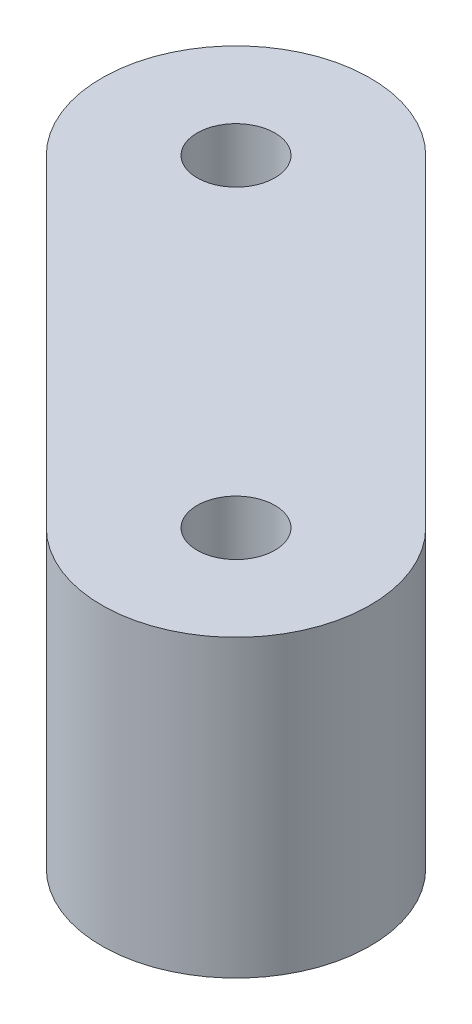
SolidWorks part; units mm, degrees
ref_plane "Alzado" through (0, 0, 0) normal (0, 0, 1) x (1, 0, 0)
ref_plane "Planta" through (0, 0, 0) normal (0, 1, 0) x (1, 0, 0)
ref_plane "Vista lateral" through (0, 0, 0) normal (1, 0, 0) x (0, 0, -1)
sketch "Croquis1" plane through (0, -33.4006, 0) normal (0, 1, 0) x (1, 0, 0)
  line L0 (-39.246, -103.383) -> (-20.7585, -84.8955) construction
  line L1 (-33.2356, -109.3934) -> (-45.2564, -97.3726) construction
  line L2 (-39.246, -103.383) -> (-42.0745, -100.5546) construction
  line L3 (-42.0745, -100.5546) -> (-35.0034, -93.4835) construction
  line L4 (-38.1854, -90.3015) -> (-26.1646, -102.3223) construction
  line L5 (-35.0034, -93.4835) -> (-29.3465, -99.1403) construction
  line L6 (-29.3465, -99.1403) -> (-36.4176, -106.2114) construction
  line L7 (-36.4176, -106.2114) -> (-42.0745, -100.5546) construction
  line L10 (-45.2564, -97.3726) -> (-33.2356, -109.3934)
  line L11 (-26.1646, -102.3223) -> (-38.1854, -90.3015)
  line L12 (-45.2564, -97.3726) -> (-33.2356, -109.3934)
  line L13 (-26.1646, -102.3223) -> (-38.1854, -90.3015)
  arc A2 (-38.1854, -90.3015) -> (-45.2564, -97.3726) centre (-41.7209, -93.837) ccw
  arc A3 (-33.2356, -109.3934) -> (-26.1646, -102.3223) centre (-29.7001, -105.8579) ccw
  arc A4 (-38.1854, -90.3015) -> (-45.2564, -97.3726) centre (-41.7209, -93.837) ccw
  arc A5 (-33.2356, -109.3934) -> (-26.1646, -102.3223) centre (-29.7001, -105.8579) ccw
  dimension "D1" = 4
  dimension "D2" = 4
  dimension "D3" = 0
extrude "Saliente-Extruir1" add sketch "Croquis1" along normal blind 11
sketch "Croquis2" plane through (0, -33.4006, 0) normal (0, -1, 0) x (1, 0, 0)
  circle A0 centre (-41.7209, 93.837) radius 1.45
  circle A1 centre (-29.7001, 105.8579) radius 1.45
  dimension "D1" = 2.9
extrude "Cortar-Extruir1" cut sketch "Croquis2" against normal blind 11
sketch "Croquis3" plane through (0, -33.4006, 0) normal (0, -1, 0) x (1, 0, 0)
  line L0 (-44.3822, 108.5192) -> (-26.4398, 90.5767) construction
  line L1 (-40.2495, 104.3865) -> (-37.4211, 107.2149)
  line L2 (-37.4211, 107.2149) -> (-26.8229, 96.6167)
  line L3 (-26.8229, 96.6167) -> (-32.4798, 90.9599)
  line L4 (-32.4798, 90.9599) -> (-43.078, 101.5581)
  line L5 (-43.078, 101.5581) -> (-40.2495, 104.3865)
  dimension "D1" = 4
  dimension "D2" = 4
extrude "Cortar-Extruir2" cut sketch "Croquis3" against normal blind 7
